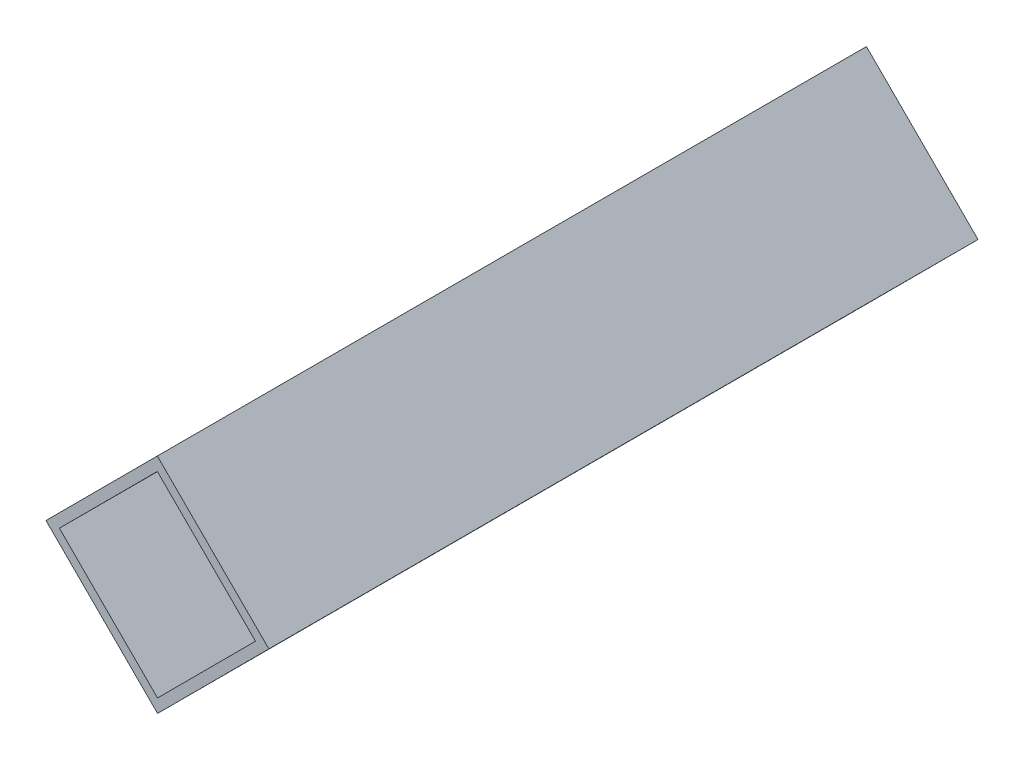
SolidWorks part; units mm, degrees
material "可鍛鑄鐵"
ref_plane "前基準面" through (0, 0, 0) normal (0, 0, 1) x (1, 0, 0)
ref_plane "上基準面" through (0, 0, 0) normal (0, 1, 0) x (1, 0, 0)
ref_plane "右基準面" through (0, 0, 0) normal (1, 0, 0) x (0, 0, -1)
sketch "草圖1" plane through (0, 0, 0) normal (0, 0, 1) x (1, 0, 0)
  line L0 (0, 0) -> (17.6938, -17.6615)
  line L1 (0, 0) -> (-17.6615, -17.6938)
  line L2 (17.6938, -17.6615) -> (0.0323, -35.3553)
  line L3 (-17.6615, -17.6938) -> (0.0323, -35.3553)
  line L4 (0.0019, -2.1213) -> (-15.5402, -17.6919)
  line L5 (0.0019, -2.1213) -> (15.5725, -17.6635)
  line L6 (-15.5402, -17.6919) -> (0.0303, -33.234)
  line L7 (15.5725, -17.6635) -> (0.0303, -33.234)
  point P0 (8.8469, -8.8308)
  dimension "D1" = 25
  dimension "D2" = 25
  dimension "D3" = 1.5
  dimension "D4" = 1.5
  dimension "D5" = 1.5
  dimension "D6" = 1.5
extrude "填料-伸長1" add sketch "草圖1" along normal blind 112.5
sketch "草圖2" plane through (0, 0, 0) normal (0.7065, 0.7078, 0) x (0.7078, -0.7065, 0)
  line L0 (25, -112.5) -> (0, -112.5) construction
  line L1 (25, -112.5) -> (25, 0) construction
  line L2 (25, 0) -> (0, 0) construction
  line L3 (0, -112.5) -> (0, 0) construction
  circle A0 centre (12.5, 59.5) radius 2.75
  circle A1 centre (12.5, 15.5) radius 2.75
  circle A2 centre (12.5, -128) radius 2.75
  circle A3 centre (12.5, -172) radius 2.75
  dimension "D1" = 5.5
  dimension "D2" = 5.5
  dimension "D4" = 128
  dimension "D5" = 12.5
  dimension "D6" = 12.5
  dimension "D7" = 5.5
  dimension "D8" = 5.5
  dimension "D9" = 44
  dimension "D10" = 128
  dimension "D11" = 12.5
  dimension "D3" = 44
